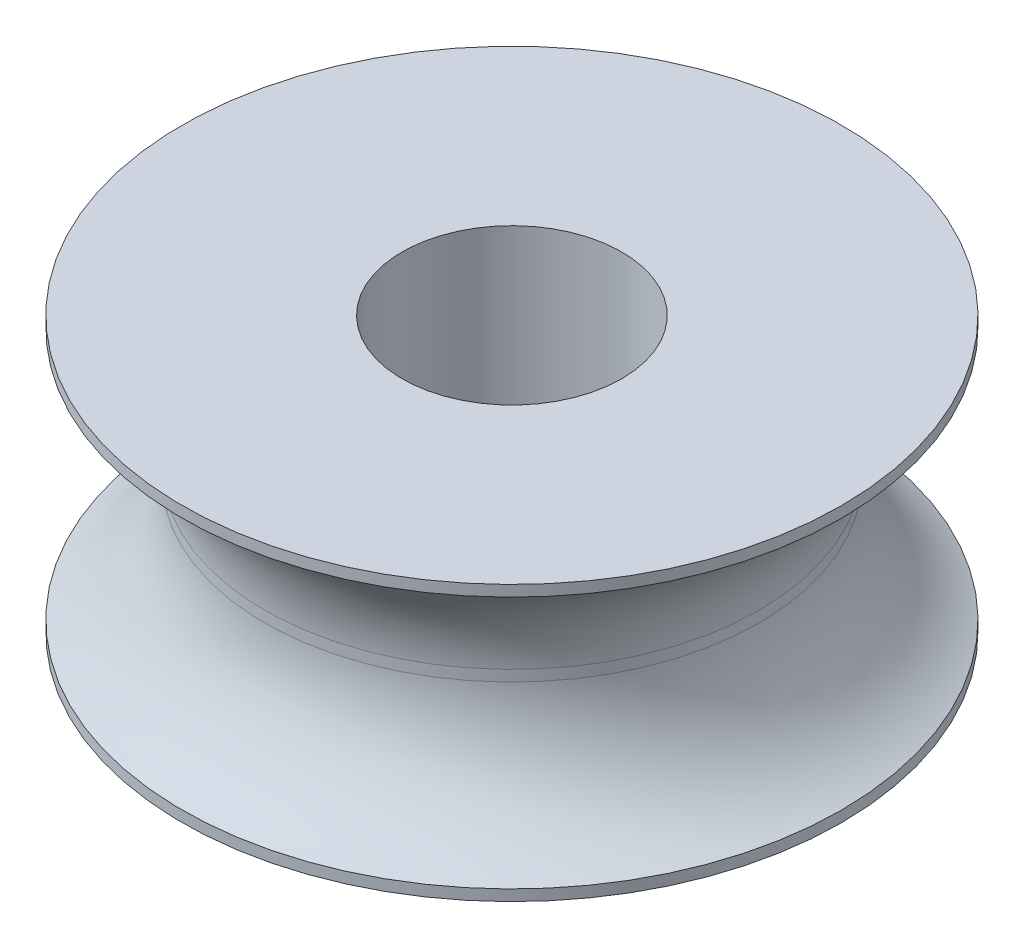
SolidWorks part; units mm, degrees
ref_plane "Front Plane" through (0, 0, 0) normal (0, 0, 1) x (1, 0, 0)
ref_plane "Top Plane" through (0, 0, 0) normal (0, 1, 0) x (1, 0, 0)
ref_plane "Right Plane" through (0, 0, 0) normal (1, 0, 0) x (0, 0, -1)
sketch "Sketch2" plane through (0, 0, 0) normal (0, 0, 1) x (1, 0, 0)
  line L0 (0, -2.5) -> (0, 2.5) construction
  line L1 (2, 2.5) -> (2, -2.5)
  line L3 (6, 2.5) -> (6, -2.5) construction
  line L5 (2, -2.5) -> (6, -2.5)
  line L6 (2, 2.5) -> (6, 2.5)
  line L7 (0, 2.5) -> (2, 2.5) construction
  line L8 (2, -2.5) -> (0, -2.5) construction
  line L9 (4.5, 2.5) -> (4.5, -2.5) construction
  line L10 (6, -2.5) -> (6, -2.3)
  line L11 (6, 2.5) -> (6, 2.3)
  line L12 (4.5, -0.1) -> (4.5, 0.1)
  arc A2 (6, 2.3) -> (6, -2.3) centre (7.0133, 0) ccw construction
  arc A3 (6, 2.3) -> (4.5, 0.1) centre (7.0148, -0.0032) ccw
  arc A4 (6, -2.3) -> (4.5, -0.1) centre (7.0148, 0.0032) cw
  point P4 (0, 0)
  point P15 (4.5, 0)
  dimension "D3" = 5
  dimension "D1" = 2
  dimension "D2" = 6
  dimension "D4" = 2.5
  dimension "D5" = 0.2
revolve "Revolve1" add sketch "Sketch2" angle 360 about L0
